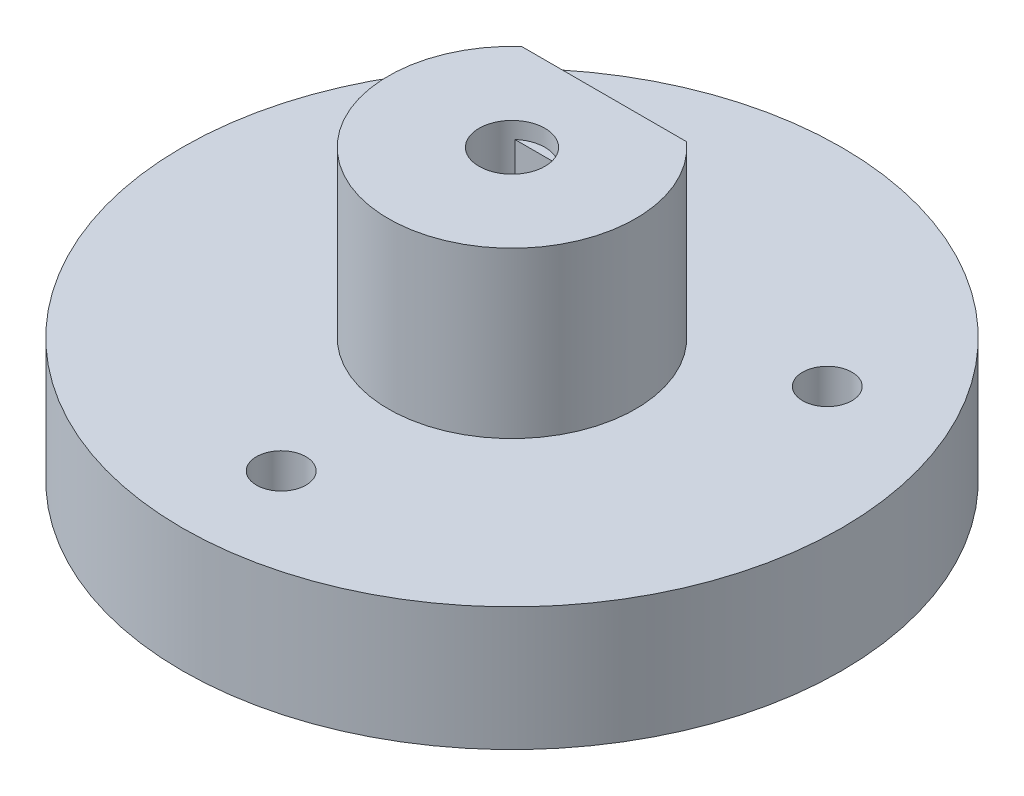
SolidWorks part; units mm, degrees
ref_plane "Front" through (0, 0, 0) normal (0, 0, 1) x (1, 0, 0)
ref_plane "Top" through (0, 0, 0) normal (0, 1, 0) x (1, 0, 0)
ref_plane "Right" through (0, 0, 0) normal (1, 0, 0) x (0, 0, -1)
sketch "Croquis1" plane through (0, 0, 0) normal (0, 1, 0) x (1, 0, 0)
  circle A0 centre (0, 0) radius 20
  dimension "D1" = 40
extrude "Saliente-Extruir1" add sketch "Croquis1" along normal blind 7.5
sketch "Croquis2" plane through (0, 7.5, 0) normal (0, 1, 0) x (1, 0, 0)
  circle A0 centre (0, 0) radius 7.5
  dimension "D1" = 15
extrude "Saliente-Extruir2" add sketch "Croquis2" along normal blind 10
sketch "Croquis5" plane through (0, 17.5, 0) normal (0, 1, 0) x (1, 0, 0)
  line L0 (-5, 5.5902) -> (5, 5.5902)
  line L1 (0, 0) -> (0, 7.5) construction
  arc A0 (-5, 5.5902) -> (5, 5.5902) centre (0, 0) cw
  circle A1 centre (0, 0) radius 7.5 construction
  dimension "D1" = 10
extrude "Cortar-Extruir1" cut sketch "Croquis5" against normal blind 10
sketch "Croquis6" plane through (0, 0, -5.5902) normal (0, 0, -1) x (-1, 0, 0)
  line L0 (0, 12.5) -> (-5, 12.5) construction
  line L1 (-5, 7.5) -> (-5, 17.5) construction
  line L2 (-5, 12.5) -> (0, 17.5) construction
  line L3 (5, 17.5) -> (-5, 17.5) construction
  line L4 (0, 17.5) -> (0, 12.5) construction
  line L5 (0, 8.4585) -> (3.5, 10.4793)
  line L6 (0, 16.4837) -> (-3.45, 14.4919) construction
  line L7 (-3.45, 14.4919) -> (-3.45, 10.5081) construction
  line L8 (-3.45, 10.5081) -> (0, 8.5163) construction
  line L9 (0, 8.5163) -> (3.45, 10.5081) construction
  line L10 (3.45, 10.5081) -> (3.45, 14.4919) construction
  line L11 (3.45, 14.4919) -> (0, 16.4837) construction
  line L12 (3.5, 10.4793) -> (3.5, 14.5207)
  line L13 (3.5, 14.5207) -> (0, 16.5415)
  line L14 (0, 16.5415) -> (-3.5, 14.5207)
  line L15 (-3.5, 14.5207) -> (-3.5, 10.4793)
  line L16 (-3.5, 10.4793) -> (0, 8.4585)
  circle A0 centre (0, 12.5) radius 3.9837 construction
  circle A1 centre (0, 12.5) radius 3.45 construction
  dimension "D1" = 3.5
  dimension "D2" = 0.05
extrude "Cortar-Extruir2" cut sketch "Croquis6" against normal blind 3
sketch "Croquis7" plane through (0, 17.5, 0) normal (0, 1, 0) x (1, 0, 0)
  line L0 (-1.3229, 1.5) -> (1.3229, 1.5)
  line L1 (0, 1.5) -> (0, -2) construction
  arc A0 (-1.3229, 1.5) -> (1.3229, 1.5) centre (0, 0) ccw
  dimension "D1" = 4
  dimension "D2" = 3.5
extrude "Cortar-Extruir3" cut sketch "Croquis7" against normal up to surface (10 mm away) up to face at (0, 7.5, 0.9549)
sketch "Croquis8" plane through (0, 0, -2.5902) normal (0, 0, -1) x (-1, 0, 0)
  line L0 (0, 12.5) -> (0, 16.5415) construction
  line L1 (0, 16.5415) -> (3.5, 12.5) construction
  line L2 (3.5, 10.4793) -> (3.5, 14.5207) construction
  line L3 (3.5, 12.5) -> (0, 12.5) construction
  circle A0 centre (0, 12.5) radius 1.875
  dimension "D1" = 3.75
extrude "Cortar-Extruir4" cut sketch "Croquis8" against normal blind 3
sketch "Croquis9" plane through (0, 7.5, 0) normal (0, 1, 0) x (1, 0, 0)
  line L0 (0, 0) -> (-12.1244, 7) construction
  line L1 (-14, 0) -> (0, 0) construction
  line L2 (-14, 0) -> (-20, 0) construction
  circle A0 centre (0, 0) radius 14 construction
  circle A1 centre (-12.1244, 7) radius 1.5
  circle A2 centre (0, 0) radius 20 construction
  circle A3 centre (12.1244, 7) radius 1.5
  circle A4 centre (0, -14) radius 1.5
  point P15 (0, 0)
  dimension "D1" = 3
  dimension "D2" = 14
  dimension "D3" = 30
  dimension "D4" = 3
extrude "Cortar-Extruir5" cut sketch "Croquis9" against normal blind 10
sketch "Croquis10" plane through (0, 17.5, 0) normal (0, 1, 0) x (1, 0, 0)
  circle A0 centre (0, 0) radius 2
  dimension "D1" = 4
extrude "Cortar-Extruir7" cut sketch "Croquis10" against normal blind 1
